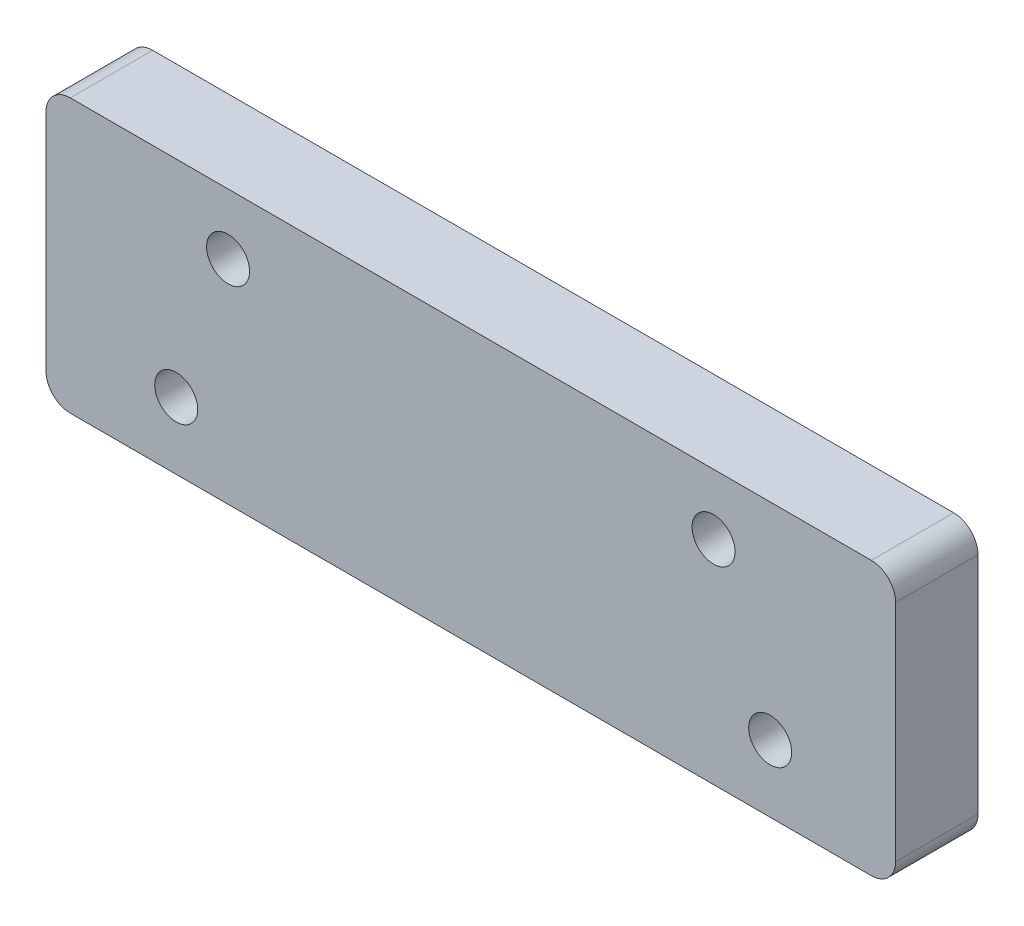
SolidWorks part; units mm, degrees
material "ABS"
ref_plane "X-Y Datum" through (0, 0, 0) normal (0, 0, 1) x (1, 0, 0)
ref_plane "X-Z Datum" through (0, 0, 0) normal (0, 1, 0) x (1, 0, 0)
ref_plane "Y-Z Datum" through (0, 0, 0) normal (1, 0, 0) x (0, 0, -1)
sketch "Sketch1" plane through (0, 0, 0) normal (0, 0, 1) x (1, 0, 0)
  line L0 (61.9, 0) -> (61.9, 14.5333) construction
  line L1 (106.35, 15.875) -> (17.45, 15.875)
  line L2 (106.35, 15.875) -> (106.35, 0)
  line L3 (106.35, 0) -> (17.45, 0)
  line L4 (17.45, 15.875) -> (17.45, 0)
  line L5 (106.35, 15.875) -> (17.45, 0) construction
  line L6 (106.35, 0) -> (17.45, 15.875) construction
  line L7 (87.225, 0) -> (36.575, 0) construction
  point P0 (61.9, 7.9375)
  point P9 (31.075, 7)
  point P13 (93.225, 7)
  dimension "D1" = 88.9
  dimension "D2" = 15.875
extrude "Boss-Extrude1" add sketch "Sketch1" against normal blind 7.62
hole_wizard "CBORE for M4 SHCS1" positions "Sketch2" profile "Sketch3" counterbore size "M4" standard "ANSI Metric" end condition through all
sketch "Sketch2" plane through (0, 0, -7.62) normal (0, 0, -1) x (-1, 0, 0)
  point P0 (-93.225, 7)
  point P3 (-31.075, 7)
sketch "Sketch3" plane through (93.225, 7, -7.62) normal (1, 0, 0) x (0, 1, 0)
  line L0 (0, 0) -> (0, 7.62)
  line L1 (0, 7.62) -> (2.25, 7.62)
  line L3 (2.25, 7.62) -> (2.25, 4)
  line L4 (2.25, 4) -> (4, 4)
  line L5 (4, 4) -> (4, 0)
  line L7 (4, 0) -> (0, 0)
  line L11 (0, -6.35) -> (0, 107.95) construction
  dimension "Thru Hole Dia." = 4.5
  dimension "Thru Hole Depth" = 7.62
  dimension "C'Bore Dia." = 8
  dimension "C'Bore Depth" = 4
sketch "Sketch4" plane through (0, 0, -7.62) normal (0, 0, -1) x (-1, 0, 0)
  line L4 (-17.45, 0) -> (-17.45, 15.875)
  line L5 (-17.45, 15.875) -> (-106.35, 15.875)
  line L6 (-106.35, 15.875) -> (-106.35, 0)
  line L7 (-106.35, 0) -> (-17.45, 0)
  line L8 (-17.45, 0) -> (-17.45, 15.875)
  line L9 (-17.45, 15.875) -> (-106.35, 15.875)
  line L10 (-106.35, 15.875) -> (-106.35, 0)
  line L11 (-106.35, 0) -> (-17.45, 0)
  circle A0 centre (-31.075, 7) radius 4 construction
  circle A1 centre (-93.225, 7) radius 4 construction
  circle A2 centre (-31.075, 7) radius 4
  circle A3 centre (-93.225, 7) radius 4
  dimension "D1" = 0
extrude "Boss-Extrude2" add sketch "Sketch4" along normal blind 1 contours L8 L9 L10 L11
sketch "Sketch5" plane through (0, 0, 0) normal (0, 0, 1) x (1, 0, 0)
  line L0 (106.35, 0) -> (106.35, 15.875) construction
  line L1 (17.45, 15.875) -> (106.35, 15.875)
  line L2 (17.45, 15.875) -> (17.45, 28.575)
  line L3 (17.45, 28.575) -> (106.35, 28.575)
  line L4 (106.35, 15.875) -> (106.35, 28.575)
  line L5 (17.45, 22.225) -> (106.35, 22.225) construction
  line L6 (61.9, 15.875) -> (61.9, 28.575) construction
  circle A0 centre (36.5, 22.225) radius 2
  circle A1 centre (87.3, 22.225) radius 2
  line M10 (106.35, 15.875) -> (17.45, 15.875)
  dimension "D2" = 4
  dimension "D1" = 12.7
  dimension "D3" = 25.4
extrude "Boss-Extrude3" add sketch "Sketch5" against normal blind 8.62 contours L4 L3 L2 A0 A1 M10 | A0 | A1
hole_wizard "M4 Clearance Hole1" positions "Sketch8" profile "Sketch9" hole size "M4" standard "ANSI Metric" end condition through all
sketch "Sketch8" plane through (0, 0, 0) normal (0, 0, 1) x (1, 0, 0)
  point P0 (36.5, 22.225)
  point P3 (87.3, 22.225)
sketch "Sketch9" plane through (36.5, 22.225, 0) normal (1, 0, 0) x (0, -1, 0)
  line L0 (0, 0) -> (0, 8.62)
  line L1 (0, 8.62) -> (2.25, 8.62)
  line L2 (2.25, 8.62) -> (2.25, 0)
  line L5 (2.25, 0) -> (0, 0)
  line L11 (0, -6.35) -> (0, 107.95) construction
  dimension "Thru Hole Dia." = 4.5
  dimension "Thru Hole Depth" = 8.62
fillet "Fillet1" radius 2.54 4 edges at (106.35, 28.575, -4.31) (106.35, 0, -4.31) (17.45, 0, -4.31) (17.45, 28.575, -4.31)
